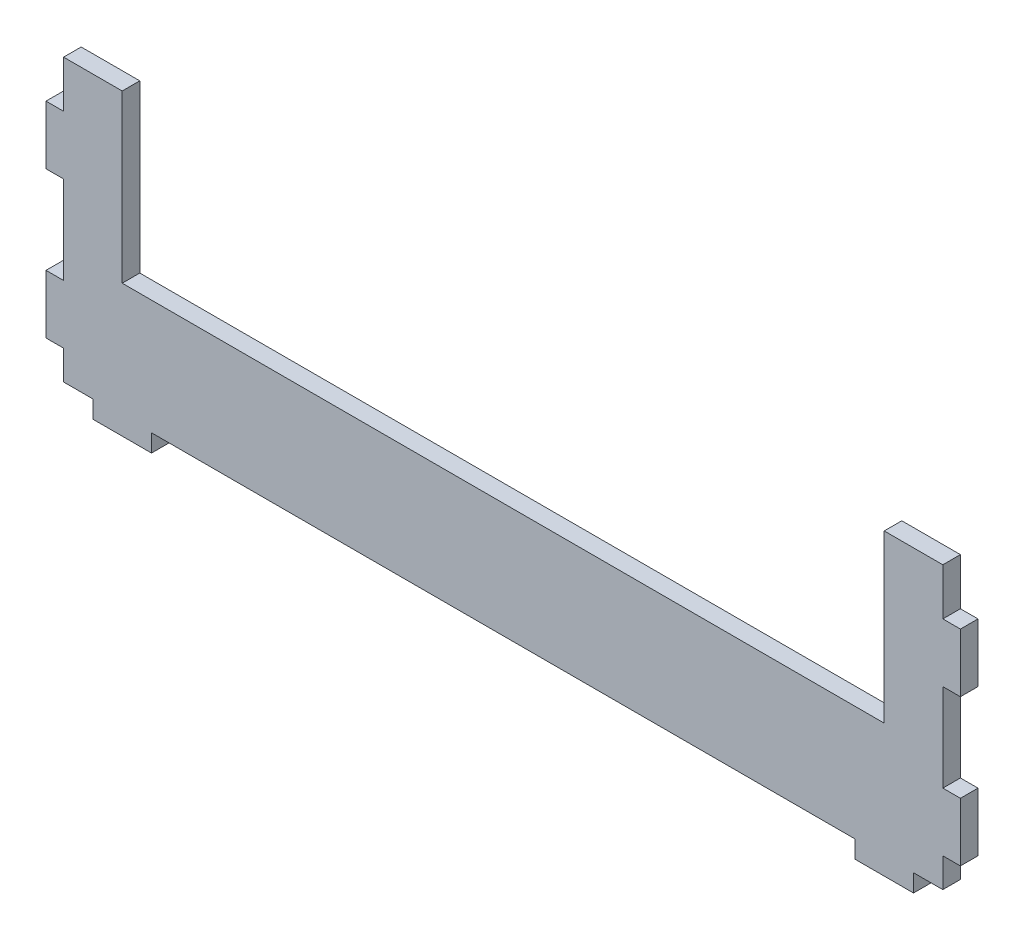
SolidWorks part; units mm, degrees
ref_plane "Front Plane" through (0, 0, 0) normal (0, 0, 1) x (1, 0, 0)
ref_plane "Top Plane" through (0, 0, 0) normal (0, 1, 0) x (1, 0, 0)
ref_plane "Right Plane" through (0, 0, 0) normal (1, 0, 0) x (0, 0, -1)
sketch "Sketch1" plane through (0, 0, 0) normal (0, 0, 1) x (1, 0, 0)
  line L0 (-195.5689, 108) -> (-189.5689, 108) construction
  line L1 (-495.5689, 6) -> (-485.5689, 6)
  line L2 (-495.5689, 6) -> (-495.5689, 16)
  line L3 (-495.5689, 102) -> (-475.5689, 102)
  line L4 (-195.5689, 6) -> (-195.5689, 16)
  line L5 (-195.5689, 86) -> (-195.5689, 102) construction
  line L6 (-401.5689, 6) -> (-465.5689, 6) construction
  line L7 (-495.5689, 86) -> (-495.5689, 102) construction
  line L8 (-189.5689, 66) -> (-189.5689, 86) construction
  line L9 (-189.5689, 86) -> (-195.5689, 86) construction
  line L11 (-195.5689, 66) -> (-189.5689, 66) construction
  line L12 (-189.5689, 16) -> (-189.5689, 36) construction
  line L13 (-189.5689, 36) -> (-195.5689, 36) construction
  line L15 (-195.5689, 16) -> (-189.5689, 16) construction
  line L17 (-225.5689, 6) -> (-225.5689, 0) construction
  line L18 (-225.5689, 0) -> (-205.5689, 0) construction
  line L19 (-205.5689, 0) -> (-205.5689, 6) construction
  line L21 (-495.5689, 86) -> (-501.5689, 86) construction
  line L22 (-501.5689, 86) -> (-501.5689, 66) construction
  line L23 (-501.5689, 66) -> (-495.5689, 66) construction
  line L25 (-495.5689, 36) -> (-501.5689, 36) construction
  line L26 (-501.5689, 36) -> (-501.5689, 16) construction
  line L27 (-501.5689, 16) -> (-495.5689, 16) construction
  line L28 (-485.5689, 0) -> (-465.5689, 0) construction
  line L29 (-465.5689, 0) -> (-465.5689, 6) construction
  line L31 (-485.5689, 6) -> (-485.5689, 0) construction
  line L32 (-189.5689, 66) -> (-189.5689, 86)
  line L33 (-189.5689, 86) -> (-195.5689, 86)
  line L35 (-195.5689, 66) -> (-189.5689, 66)
  line L36 (-189.5689, 16) -> (-189.5689, 36)
  line L37 (-189.5689, 36) -> (-195.5689, 36)
  line L39 (-195.5689, 16) -> (-189.5689, 16)
  line L41 (-225.5689, 6) -> (-225.5689, 0)
  line L42 (-225.5689, 0) -> (-205.5689, 0)
  line L43 (-205.5689, 0) -> (-205.5689, 6)
  line L45 (-495.5689, 86) -> (-501.5689, 86)
  line L46 (-501.5689, 86) -> (-501.5689, 66)
  line L47 (-501.5689, 66) -> (-495.5689, 66)
  line L49 (-495.5689, 36) -> (-501.5689, 36)
  line L50 (-501.5689, 36) -> (-501.5689, 16)
  line L51 (-501.5689, 16) -> (-495.5689, 16)
  line L52 (-485.5689, 0) -> (-465.5689, 0)
  line L53 (-465.5689, 0) -> (-465.5689, 6)
  line L55 (-485.5689, 6) -> (-485.5689, 0)
  line L56 (-205.5689, 6) -> (-195.5689, 6)
  line L57 (-195.5689, 36) -> (-195.5689, 66)
  line L58 (-195.5689, 86) -> (-195.5689, 102)
  line L59 (-465.5689, 6) -> (-225.5689, 6)
  line L60 (-495.5689, 36) -> (-495.5689, 66)
  line L61 (-495.5689, 86) -> (-495.5689, 102)
  line L62 (-215.5689, 102) -> (-195.5689, 102)
  line L64 (-475.5689, 102) -> (-475.5689, 45.2)
  line L65 (-475.5689, 45.2) -> (-215.5689, 45.2)
  line L66 (-215.5689, 102) -> (-215.5689, 45.2)
  line L69 (-450.5689, 75.4) -> (-450.5689, 75.2) construction
  line L70 (-469.8189, 65.2) -> (-219.8189, 65.2) construction
  line L71 (-475.5689, 102) -> (-215.5689, 102) construction
  line L72 (-345.5689, 45.2) -> (-345.5689, 102) construction
  dimension "D1" = 6
  dimension "D2" = 25
  dimension "D3" = 20
extrude "Boss-Extrude1" add sketch "Sketch1" along normal up to surface (6 mm away)
